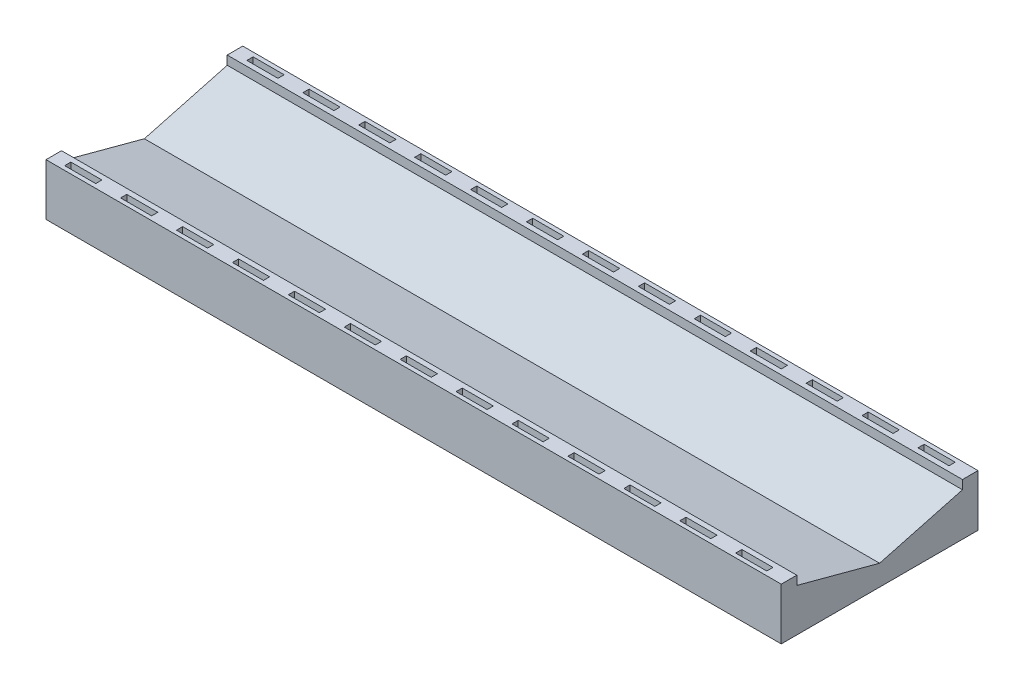
SolidWorks part; units mm, degrees
other "Markup1"
sketch "Sketch3" plane through (0, 2.5, 0) normal (-0.0318, 0.9983, 0.0497) x (0.9118, 0.0493, -0.4077)
ref_plane "Front Plane" through (0, 0, 0) normal (0, 0, 1) x (1, 0, 0)
ref_plane "Top Plane" through (0, 0, 0) normal (0, 1, 0) x (1, 0, 0)
ref_plane "Right Plane" through (0, 0, 0) normal (1, 0, 0) x (0, 0, -1)
sketch "Sketch1" plane through (0, 0, 0) normal (0, 1, 0) x (1, 0, 0)
  line L1 (0, 0) -> (38, 0)
  line L2 (0, 0) -> (0, 9.5)
  line L3 (0, 9.5) -> (38, 9.5)
  line L4 (38, 0) -> (38, 9.5)
  dimension "D1" = 38
  dimension "D2" = 9.5
extrude "Boss-Extrude1" add sketch "Sketch1" along normal blind 2.5
sketch "Sketch2" plane through (0, 2.5, 0) normal (0, 1, 0) x (1, 0, 0)
  line L0 (0, 9.5) -> (0, 0) construction
  line L1 (0.5, 0.5) -> (2, 0.5)
  line L2 (0.5, 0.5) -> (0.5, 0.2)
  line L3 (0.5, 0.2) -> (2, 0.2)
  line L4 (2, 0.5) -> (2, 0.2)
  line L5 (0, 0) -> (38, 0) construction
  dimension "D1" = 1.5
  dimension "D2" = 0.3
  dimension "D3" = 0.5
  dimension "D4" = 0.2
extrude "Cut-Extrude1" cut sketch "Sketch2" against normal blind 2
pattern_linear "LPattern1" count 14 spacing 2.7 along (1, 0, 0) count 2 spacing 8.8 along (0, 0, -1) of "Cut-Extrude1"
sketch "Sketch4" plane through (38, 0, 0) normal (1, 0, 0) x (0, 0, -1)
  line L5 (0.75, 2.5) -> (0.75, 2.0718)
  line L6 (0, 2.5) -> (9.5, 2.5) construction
  line L7 (0.75, 2.0718) -> (4.75, 1)
  line L8 (4.75, 1) -> (8.75, 2.0718)
  line L9 (8.75, 2.0718) -> (8.75, 2.5)
  line L10 (4.75, 2.5) -> (4.75, 1) construction
  dimension "D1" = 0.25
  dimension "D2" = 0.25
  dimension "D3" = 150
  dimension "D4" = 1.5
extrude "Cut-Extrude2" cut sketch "Sketch4" against normal through all and the other way through all
sketch "Sketch5" plane through (0, 0, 0) normal (-1, 0, 0) x (0, 0, 1)
  line L9 (-0.75, 2.5) -> (-0.75, 2.0718)
  line L10 (-0.75, 2.0718) -> (-4.75, 1)
  line L11 (-4.75, 1) -> (-8.75, 2.0718)
  line L12 (-8.75, 2.0718) -> (-8.75, 2.5)
  line L13 (-8.75, 2.5) -> (-9.5, 2.5)
  line L14 (-9.5, 2.5) -> (-9.5, 0)
  line L15 (-9.5, 0) -> (0, 0)
  line L16 (0, 0) -> (0, 2.5)
  line L17 (0, 2.5) -> (-0.75, 2.5)
  line L18 (-0.75, 2.5) -> (-0.75, 2.0718)
  line L19 (-0.75, 2.0718) -> (-4.75, 1)
  line L20 (-4.75, 1) -> (-8.75, 2.0718)
  line L21 (-8.75, 2.0718) -> (-8.75, 2.5)
  line L22 (-8.75, 2.5) -> (-9.5, 2.5)
  line L23 (-9.5, 2.5) -> (-9.5, 0)
  line L24 (-9.5, 0) -> (0, 0)
  line L25 (0, 0) -> (0, 2.5)
  line L26 (0, 2.5) -> (-0.75, 2.5)
  dimension "D1" = 0
extrude "Cut-Extrude3" cut sketch "Sketch5" against normal blind 2.5
